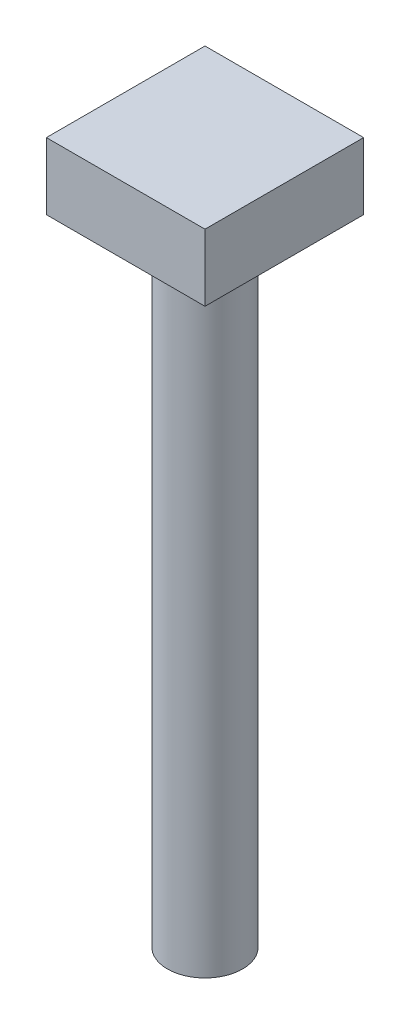
SolidWorks part; units mm, degrees
ref_plane "Front Plane" through (0, 0, 0) normal (0, 0, 1) x (1, 0, 0)
ref_plane "Top Plane" through (0, 0, 0) normal (0, 1, 0) x (1, 0, 0)
ref_plane "Right Plane" through (0, 0, 0) normal (1, 0, 0) x (0, 0, -1)
sketch "Sketch3" plane through (0, 0, 0) normal (0, 1, 0) x (1, 0, 0)
  line L1 (-9.5, 9.5) -> (9.5, 9.5)
  line L2 (-9.5, 9.5) -> (-9.5, -9.5)
  line L3 (-9.5, -9.5) -> (9.5, -9.5)
  line L4 (9.5, 9.5) -> (9.5, -9.5)
  line L5 (-9.5, 9.5) -> (9.5, -9.5) construction
  line L6 (-9.5, -9.5) -> (9.5, 9.5) construction
  point P0 (0, 0)
  dimension "D1" = 19
  dimension "D2" = 19
extrude "Boss-Extrude1" add sketch "Sketch3" along normal blind 8
sketch "Sketch4" plane through (0, 0, 0) normal (0, 1, 0) x (1, 0, 0)
  circle A0 centre (0, 0) radius 4.5
  dimension "D1" = 9
extrude "Boss-Extrude2" add sketch "Sketch4" against normal blind 76
